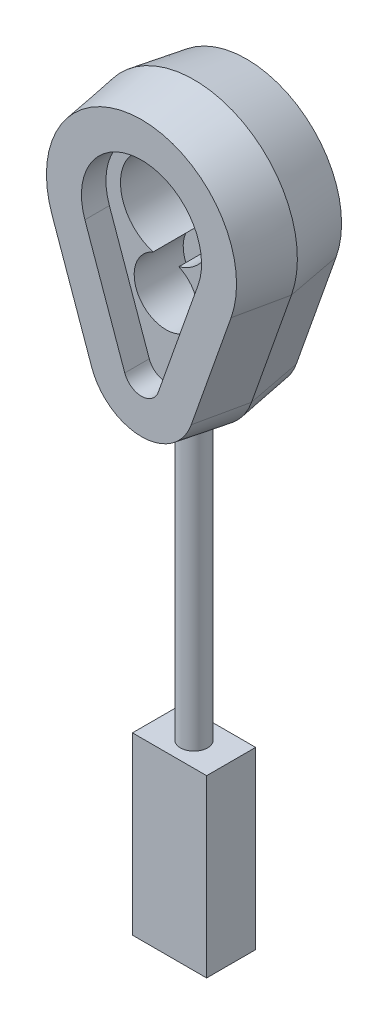
SolidWorks part; units mm, degrees
ref_plane "Front Plane" through (0, 0, 0) normal (0, 0, 1) x (1, 0, 0)
ref_plane "Top Plane" through (0, 0, 0) normal (0, 1, 0) x (1, 0, 0)
ref_plane "Right Plane" through (0, 0, 0) normal (1, 0, 0) x (0, 0, -1)
sketch "Sketch1" plane through (0, 0, 0) normal (0, 0, 1) x (1, 0, 0)
  line L0 (0, 21.8213) -> (0, -14.5795) construction
  line L1 (-7.0704, 6.5999) -> (-4.177, -1.5771)
  line L2 (7.0704, 6.5999) -> (4.177, -1.5771)
  arc A0 (-7.0704, 6.5999) -> (7.0704, 6.5999) centre (0, 9.1018) cw
  arc A1 (-4.177, -1.5771) -> (4.177, -1.5771) centre (0, -0.0991) ccw
  dimension "D1" = 7.5
extrude "Boss-Extrude3" add sketch "Sketch1" along normal mid plane 7.62 draft 9
sketch "Sketch3" plane through (0, 0, 3.81) normal (0, 0, 1) x (1, 0, 0)
  line L6 (-4.107, 7.6485) -> (-1.2136, -0.5285)
  line L7 (1.2136, -0.5285) -> (4.107, 7.6485)
  line L8 (-4.107, 7.6485) -> (-1.2136, -0.5285)
  line L9 (1.2136, -0.5285) -> (4.107, 7.6485)
  arc A6 (4.107, 7.6485) -> (-4.107, 7.6485) centre (0, 9.1018) ccw
  arc A7 (-1.2136, -0.5285) -> (1.2136, -0.5285) centre (0, -0.0991) ccw
  arc A8 (4.107, 7.6485) -> (-4.107, 7.6485) centre (0, 9.1018) ccw
  arc A9 (-1.2136, -0.5285) -> (1.2136, -0.5285) centre (0, -0.0991) ccw
  dimension "D1" = 2.54
extrude "Cut-Extrude1" cut sketch "Sketch3" against normal blind 1.778 contours A8 L8 A9 L9
sketch "Sketch4" plane through (0, 0, 2.032) normal (0, 0, 1) x (1, 0, 0)
  arc A0 (0.9305, 6.3283) -> (-0.9305, 6.3283) centre (0, 9.498) ccw
  arc A1 (-0.9305, 6.3283) -> (0.9305, 6.3283) centre (0, 4.2162) ccw
  point P4 (0, 0)
extrude "Cut-Extrude2" cut sketch "Sketch4" against normal blind 3.556
ref_plane "Plane1" through (0, -24.9256, 0) normal (0, 1, 0) x (1, 0, 0)
sketch "Sketch6" plane through (0, -24.9256, 0) normal (0, 1, 0) x (1, 0, 0)
  circle A0 centre (0, 0) radius 0.9841
extrude "Boss-Extrude4" add sketch "Sketch6" along normal up to next
sketch "Sketch7" plane through (0, 0, 0) normal (0, 0, 1) x (1, 0, 0)
  line L0 (0.0035, -20.157) -> (0.0035, -24.894) construction
  line L1 (-2.6871, -24.894) -> (2.694, -24.894)
  line L2 (-2.6871, -24.894) -> (-2.6871, -37.6076)
  line L3 (-2.6871, -37.6076) -> (2.694, -37.6076)
  line L4 (2.694, -24.894) -> (2.694, -37.6076)
  point P6 (0, 0)
sketch "Sketch8" plane through (0, 0, 0) normal (0, 0, 1) x (1, 0, 0)
extrude "Boss-Extrude5" add sketch "Sketch7" along normal mid plane 3.556
sketch "Sketch9" plane through (0, 0, 1.778) normal (0, 0, 1) x (1, 0, 0)
  line L0 (0.994, -37.3352) -> (0.994, -25.6267) construction
  text T1 "GIKI Rocket Engineering Team" height 0.635
